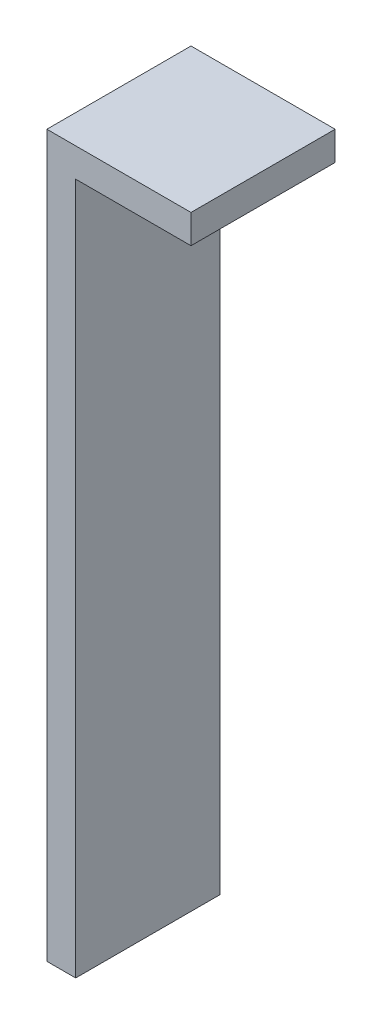
SolidWorks part; units mm, degrees
material "Copper"
ref_plane "Front Plane" through (0, 0, 0) normal (0, 0, 1) x (1, 0, 0)
ref_plane "Top Plane" through (0, 0, 0) normal (0, 1, 0) x (1, 0, 0)
ref_plane "Right Plane" through (0, 0, 0) normal (1, 0, 0) x (0, 0, -1)
sketch "Sketch1" plane through (0, 0, 0) normal (0, 0, 1) x (1, 0, 0)
  line L0 (0, 0) -> (-1, 0)
  line L1 (-1, 0) -> (-1, -5)
  line L2 (-1, -5) -> (-0.8, -5)
  line L3 (-0.8, -5) -> (-0.8, -0.2)
  line L4 (-0.8, -0.2) -> (0, -0.2)
  line L5 (0, -0.2) -> (0, 0)
  dimension "D1" = 0.2
  dimension "D2" = 5
  dimension "D3" = 1
extrude "Boss-Extrude1" add sketch "Sketch1" along normal mid plane 1
